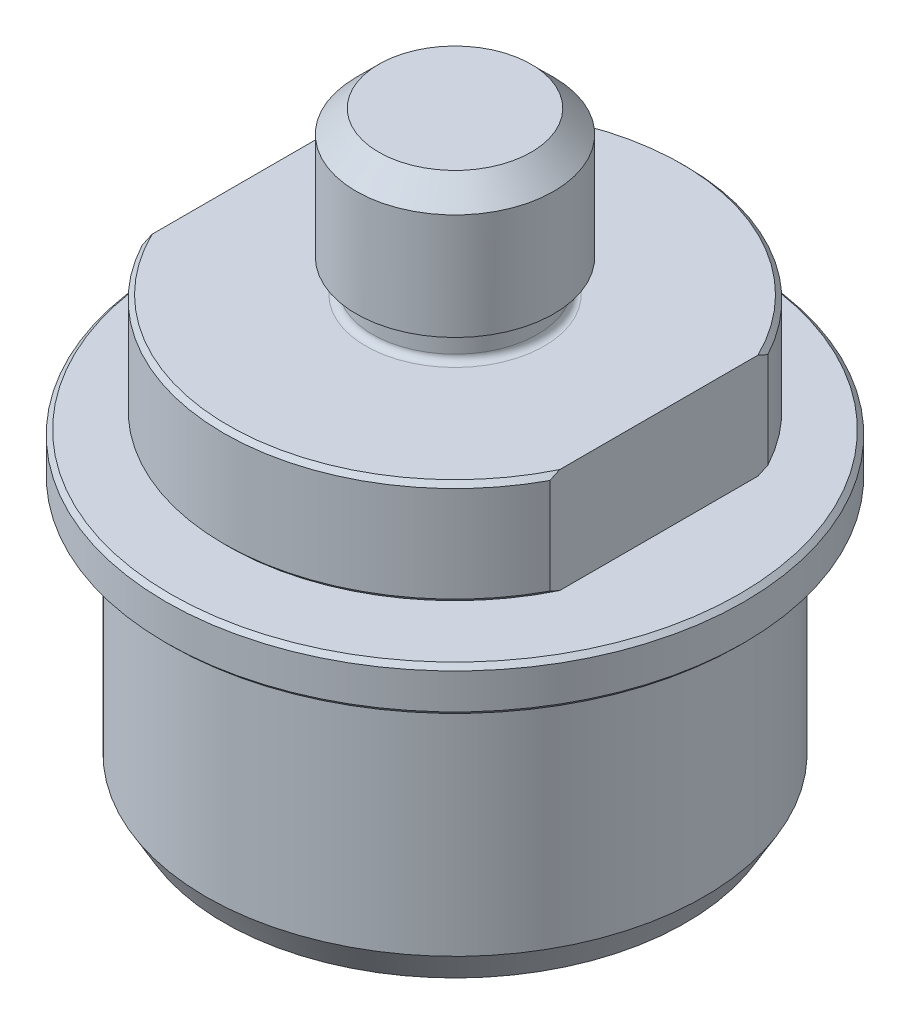
SolidWorks part; units mm, degrees
ref_plane "Front Plane" through (0, 0, 0) normal (0, 0, 1) x (1, 0, 0)
ref_plane "Top Plane" through (0, 0, 0) normal (0, 1, 0) x (1, 0, 0)
ref_plane "Right Plane" through (0, 0, 0) normal (1, 0, 0) x (0, 0, -1)
sketch "Sketch1" plane through (0, 0, 0) normal (0, 0, 1) x (1, 0, 0)
  line L0 (0, 18.161) -> (0, -30.2006)
  line L1 (0, 18.161) -> (11.1125, 18.161)
  line L2 (11.1125, 18.161) -> (11.1125, 3.683)
  line L3 (10.033, 0) -> (25.9969, 0)
  line L4 (25.9969, 0) -> (25.9969, -11.7856)
  line L5 (25.9969, -11.7856) -> (17.9705, -11.7856)
  line L6 (17.9705, -11.7856) -> (17.9705, -45.5676)
  line L7 (17.9705, -50.038) -> (14.1478, -50.038)
  line L8 (0, 18.161) -> (0, 50.8132) construction
  line L9 (11.1125, 3.683) -> (9.271, 3.683)
  line L10 (9.271, 3.683) -> (9.271, 0.762)
  line L11 (12.6238, -48.514) -> (12.6238, -38.1254)
  line L12 (12.6238, -38.1254) -> (4.699, -30.2006)
  line L13 (4.699, -30.2006) -> (0, -30.2006)
  line L14 (17.9705, -48.1076) -> (17.9705, -50.038)
  arc A0 (17.9705, -45.5676) -> (17.9705, -48.1076) centre (17.9705, -46.8376) ccw
  arc A1 (14.1478, -50.038) -> (12.6238, -48.514) centre (14.1478, -48.514) cw
  arc A2 (10.033, 0) -> (9.271, 0.762) centre (10.033, 0.762) cw
  dimension "D14" = 1.27
  dimension "D15" = 1.524
  dimension "D16" = 0.762
  dimension "D1" = 22.225
  dimension "D2" = 18.161
  dimension "D3" = 11.7856
  dimension "D4" = 50.038
  dimension "D5" = 35.941
  dimension "D6" = 51.9938
  dimension "D7" = 3.683
  dimension "D8" = 18.542
  dimension "D9" = 25.2476
  dimension "D10" = 11.9126
  dimension "D11" = 45
  dimension "D12" = 9.398
  dimension "D13" = 1.9304
revolve "Revolve1" add sketch "Sketch1" angle 360 about L8
chamfer "Chamfer1" distance 0.508 angle 45 2 edges at (0, -11.7856, -25.9969) (0, 0, -25.9969)
chamfer "Chamfer2" distance 2.54 angle 45 1 edges at (0, 18.161, -11.1125)
sketch "Sketch4" plane through (0, 0, 0) normal (0, 1, 0) x (1, 0, 0)
  line L0 (-22.9235, 12.2618) -> (-22.9235, -12.2618)
  line L1 (22.9235, 12.2618) -> (22.9235, -12.2618)
  circle A0 centre (0, 0) radius 25.9969 construction
  arc A1 (22.9235, -12.2618) -> (22.9235, 12.2618) centre (0, 0) ccw
  arc A2 (-22.9235, 12.2618) -> (-22.9235, -12.2618) centre (0, 0) ccw
  dimension "D1" = 22.9235
  dimension "D2" = 22.9235
extrude "Cut-Extrude1" cut sketch "Sketch4" against normal through all
sketch "Sketch2" plane through (0, 0, 0) normal (0, 0, 1) x (1, 0, 0)
  line L0 (18.0213, -13.1572) -> (18.0213, -40.8178)
  line L1 (20.955, -48.2092) -> (25.9504, -48.2092)
  line L2 (25.9504, -48.2092) -> (28.0035, -44.6532)
  line L3 (28.0035, -44.6532) -> (28.0035, -18.923)
  line L4 (28.7655, -18.161) -> (32.512, -18.161)
  line L5 (32.512, -18.161) -> (32.512, -13.1572)
  line L6 (32.512, -13.1572) -> (18.0213, -13.1572)
  line L7 (0, 0) -> (0, 33.0062) construction
  line L8 (25.4889, 0) -> (-25.4889, 0) construction
  line L9 (17.9705, -45.5676) -> (17.9705, -11.7856) construction
  line L11 (20.955, -48.2092) -> (20.955, -41.8338)
  line L12 (19.939, -40.8178) -> (18.0213, -40.8178)
  line L13 (17.9705, -45.5676) -> (-17.9705, -45.5676) construction
  line L14 (-17.9705, -50.038) -> (17.9705, -50.038) construction
  arc A0 (20.955, -41.8338) -> (19.939, -40.8178) centre (19.939, -41.8338) ccw
  arc A1 (28.0035, -18.923) -> (28.7655, -18.161) centre (28.7655, -18.923) cw
  dimension "D13" = 1.016
  dimension "D14" = 0.762
  dimension "D1" = 35.052
  dimension "D2" = 5.0038
  dimension "D3" = 56.007
  dimension "D4" = 65.024
  dimension "D5" = 3.556
  dimension "D6" = 30
  dimension "D7" = 51.9009
  dimension "D8" = 18.161
  dimension "D9" = 0.0508
  dimension "D10" = 4.7498
  dimension "D11" = 1.8288
  dimension "D12" = 41.91
revolve "Revolve2" add sketch "Sketch2" angle 360 about L7
chamfer "Chamfer3" distance 0.508 angle 45 2 edges at (0, -13.1572, -32.512) (0, -18.161, -32.512)
sketch "Sketch3" plane through (0, 0, 0) normal (0, 0, 1) x (1, 0, 0)
  line L1 (0, 0) -> (0, -31.4929) construction
  circle A0 centre (17.9705, -46.8376) radius 1.2192
  arc A2 (17.9705, -45.5676) -> (17.9705, -48.1076) centre (17.9705, -46.8376) ccw construction
  dimension "D1" = 0.0508
revolve "Revolve3" add sketch "Sketch3" angle 330 about L1
